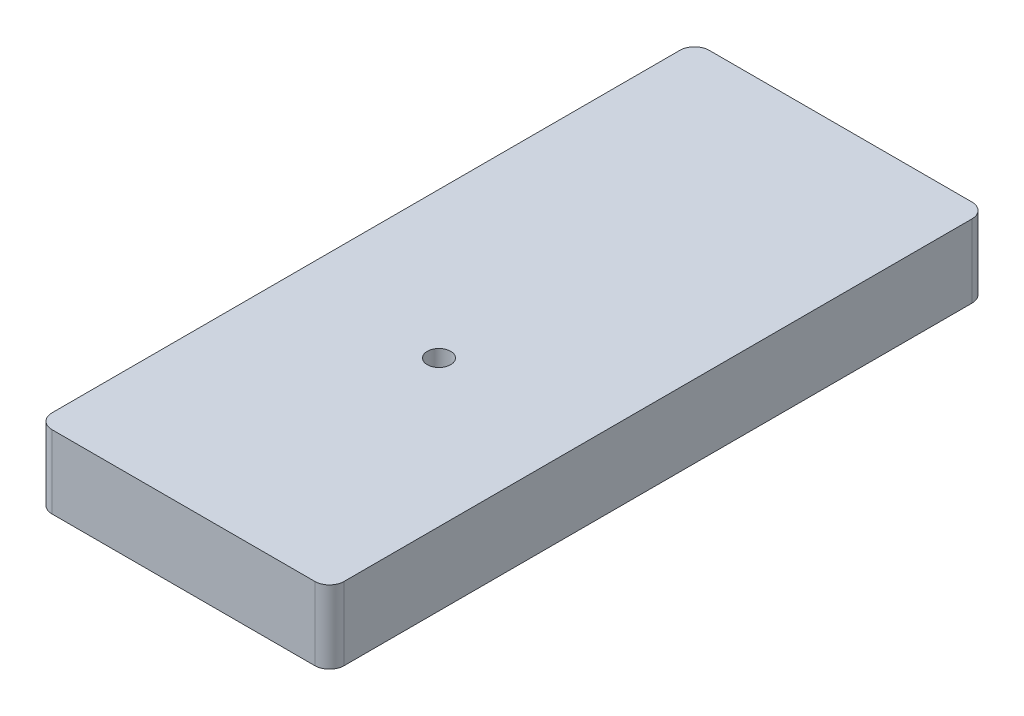
SolidWorks part; units mm, degrees
ref_plane "Plan de face" through (0, 0, 0) normal (0, 0, 1) x (1, 0, 0)
ref_plane "Plan de dessus" through (0, 0, 0) normal (0, 1, 0) x (1, 0, 0)
ref_plane "Plan de droite" through (0, 0, 0) normal (1, 0, 0) x (0, 0, -1)
sketch "Esquisse1" plane through (0, 0, 0) normal (0, 1, 0) x (1, 0, 0)
  line L0 (-6.427, 0) -> (109.1376, 0) construction
  line L1 (0, -7.0221) -> (0, 103.9034) construction
  line L2 (53, -7.0221) -> (53, 103.9034) construction
  line L3 (-6.427, 40) -> (85.7278, 40) construction
  line L4 (-6.427, 90) -> (109.1376, 90) construction
  line L5 (13, 2) -> (13, 88)
  line L6 (33, 59.5746) -> (33, 22.2331) construction
  line L7 (15, 0) -> (51, 0)
  line L8 (53, 88) -> (53, 2)
  line L9 (45.7647, 35) -> (8.4232, 35) construction
  line L10 (13, 103.9034) -> (13, -7.0221) construction
  line L11 (15, 90) -> (51, 90)
  arc A0 (51, 90) -> (53, 88) centre (51, 88) cw
  arc A1 (15, 0) -> (13, 2) centre (15, 2) cw
  arc A2 (51, 0) -> (53, 2) centre (51, 2) ccw
  arc A3 (15, 90) -> (13, 88) centre (15, 88) ccw
  circle A4 centre (33, 35) radius 1.6
  point P12 (53, 90)
  point P15 (13, 0)
  point P26 (13, 90)
  dimension "D3" = 2
  dimension "D7" = 5
  dimension "D5" = 2
  dimension "D1" = 90
  dimension "D2" = 40
  dimension "D4" = 50
  dimension "D6" = 20
extrude "Extrusion1" add sketch "Esquisse1" along normal blind 10
sketch "Esquisse2" plane through (0, 0, 0) normal (0, -1, 0) x (1, 0, 0)
  line L0 (57.4636, -79) -> (-27.3834, -79) construction
  line L1 (-17.6242, -59.5) -> (57.4636, -59.5) construction
  line L2 (57.4636, -40) -> (-27.3834, -40) construction
  line L3 (57.4636, -20) -> (-27.3834, -20) construction
  line L4 (53, -103.2829) -> (53, 4.7947) construction
  line L5 (57.4636, -10) -> (-27.3834, -10) construction
  line L6 (48, -121.675) -> (48, 4.7947) construction
  line L7 (42, -111.2442) -> (42, 4.7947) construction
  line L8 (57.4636, -90) -> (-27.3834, -90) construction
  line L9 (57.4636, -85) -> (-27.3834, -85) construction
  line L10 (33, -121.675) -> (33, -69.6956) construction
  line L11 (41, -103.2829) -> (41, -69.6956) construction
  line L12 (57.4636, -49.5) -> (28.6431, -49.5) construction
  line L13 (37.3159, -82) -> (19.2671, -82) construction
  line L14 (45, -57.6837) -> (45, -3.061) construction
  line L15 (42, -49.5) -> (49.9748, -57.4748) construction
  line L16 (41, -82.7373) -> (41, -81.2627)
  line L17 (41, -85) -> (33.7489, -77.7489) construction
  line L18 (45.7373, -49.5) -> (44.2627, -49.5)
  line L19 (45.7373, -69.5) -> (44.2627, -69.5)
  line L20 (25, -82.7373) -> (25, -81.2627)
  line L21 (38.7373, -85) -> (27.2627, -85)
  line L22 (38.7373, -79) -> (27.2627, -79)
  line L23 (48, -67.2373) -> (48, -51.7627)
  line L24 (42, -67.2373) -> (42, -51.7627)
  line L25 (24, -67.2373) -> (24, -51.7627)
  line L26 (18, -67.2373) -> (18, -51.7627)
  line L27 (20.2627, -69.5) -> (21.7373, -69.5)
  line L28 (20.2627, -49.5) -> (21.7373, -49.5)
  line L29 (57.4636, -7) -> (6.2084, -7) construction
  line L30 (57.4636, -23) -> (6.2084, -23) construction
  arc A0 (44.2627, -49.5) -> (42, -51.7627) centre (43.1314, -50.6314) ccw
  arc A1 (38.7373, -85) -> (41, -82.7373) centre (39.8686, -83.8686) ccw
  arc A2 (38.7373, -79) -> (41, -81.2627) centre (39.8686, -80.1314) cw
  arc A3 (27.2627, -85) -> (25, -82.7373) centre (26.1314, -83.8686) cw
  arc A4 (27.2627, -79) -> (25, -81.2627) centre (26.1314, -80.1314) ccw
  arc A5 (45.7373, -49.5) -> (48, -51.7627) centre (46.8686, -50.6314) cw
  arc A6 (44.2627, -69.5) -> (42, -67.2373) centre (43.1314, -68.3686) cw
  arc A7 (45.7373, -69.5) -> (48, -67.2373) centre (46.8686, -68.3686) ccw
  arc A8 (20.2627, -69.5) -> (18, -67.2373) centre (19.1314, -68.3686) cw
  arc A9 (21.7373, -69.5) -> (24, -67.2373) centre (22.8686, -68.3686) ccw
  arc A10 (20.2627, -49.5) -> (18, -51.7627) centre (19.1314, -50.6314) ccw
  arc A11 (21.7373, -49.5) -> (24, -51.7627) centre (22.8686, -50.6314) cw
  circle A14 centre (21, -7) radius 1.1
  circle A15 centre (21, -23) radius 1.1
  dimension "D15" = 3
  dimension "D1" = 19.5
  dimension "D2" = 20
  dimension "D3" = 10
  dimension "D4" = 6
  dimension "D5" = 5
  dimension "D6" = 5
  dimension "D7" = 6
  dimension "D8" = 15
  dimension "D9" = 8
  dimension "D10" = 10
  dimension "D11" = 3
  dimension "D12" = 3
  dimension "D13" = 45
  dimension "D14" = 45
  dimension "D16" = 3
extrude "Enlèv. mat.-Extru.1" cut sketch "Esquisse2" against normal blind 4
